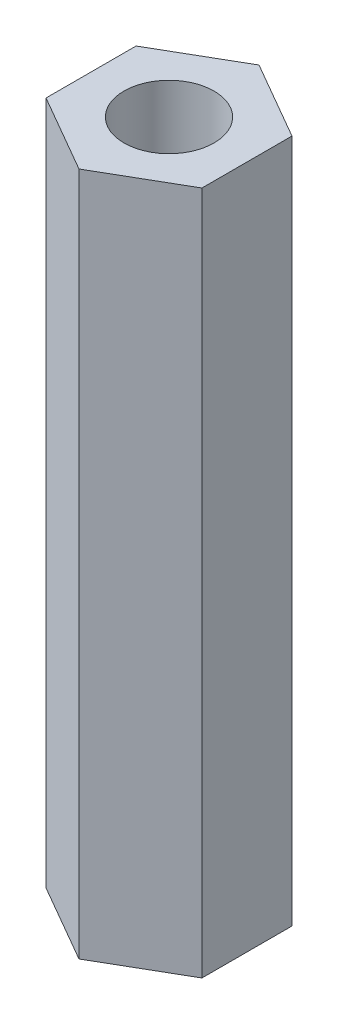
SolidWorks part; units mm, degrees
ref_plane "Face" through (0, 0, 0) normal (0, 0, 1) x (1, 0, 0)
ref_plane "Dessus" through (0, 0, 0) normal (0, 1, 0) x (1, 0, 0)
ref_plane "Droite" through (0, 0, 0) normal (1, 0, 0) x (0, 0, -1)
sketch "Esquisse1" plane through (0, 0, 0) normal (0, 1, 0) x (1, 0, 0)
  line L0 (0, 0) -> (0, 5.5688) construction
  line L1 (0, 5) -> (-4.3301, 2.5)
  line L2 (-4.3301, 2.5) -> (-4.3301, -2.5)
  line L3 (-4.3301, -2.5) -> (0, -5)
  line L4 (0, -5) -> (4.3301, -2.5)
  line L5 (4.3301, -2.5) -> (4.3301, 2.5)
  line L6 (4.3301, 2.5) -> (0, 5)
  circle A0 centre (0, 0) radius 4.3301 construction
  circle A1 centre (0, 0) radius 2.5
  dimension "D1" = 10
  dimension "D2" = 5
extrude "Extrusion1" add sketch "Esquisse1" along normal blind 38
